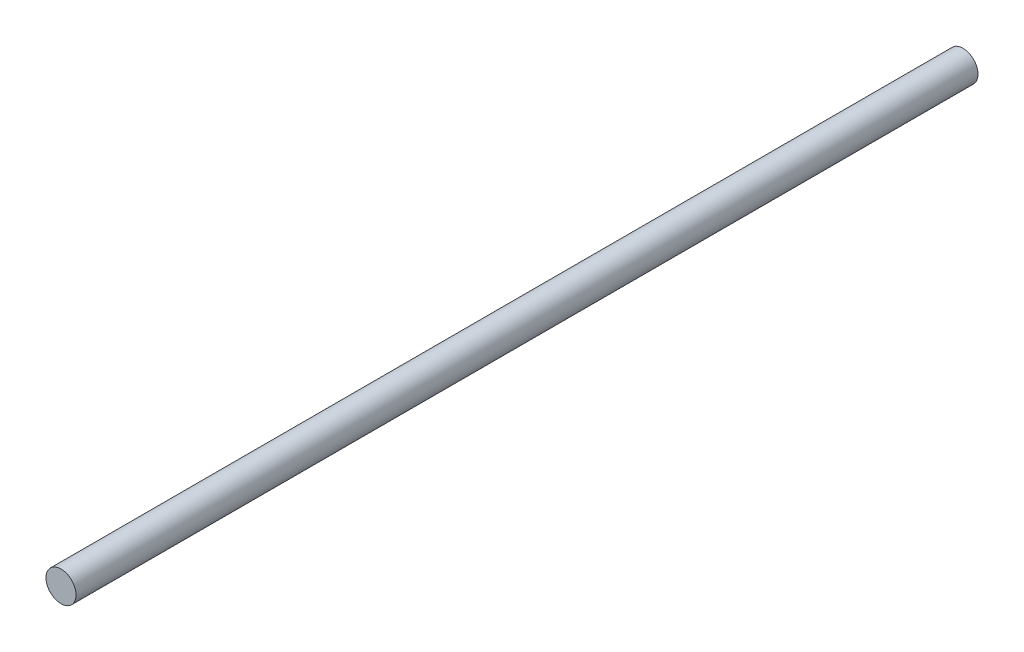
SolidWorks part; units mm, degrees
ref_plane "Plano frontal" through (0, 0, 0) normal (0, 0, 1) x (1, 0, 0)
ref_plane "Plano superior" through (0, 0, 0) normal (0, 1, 0) x (1, 0, 0)
ref_plane "Plano direito" through (0, 0, 0) normal (1, 0, 0) x (0, 0, -1)
sketch "Esboço1" plane through (0, 0, 0) normal (0, 0, 1) x (1, 0, 0)
  circle A0 centre (0, 0) radius 3
  dimension "D1" = 6
extrude "Ressalto-extrusão1" add sketch "Esboço1" along normal blind 180
